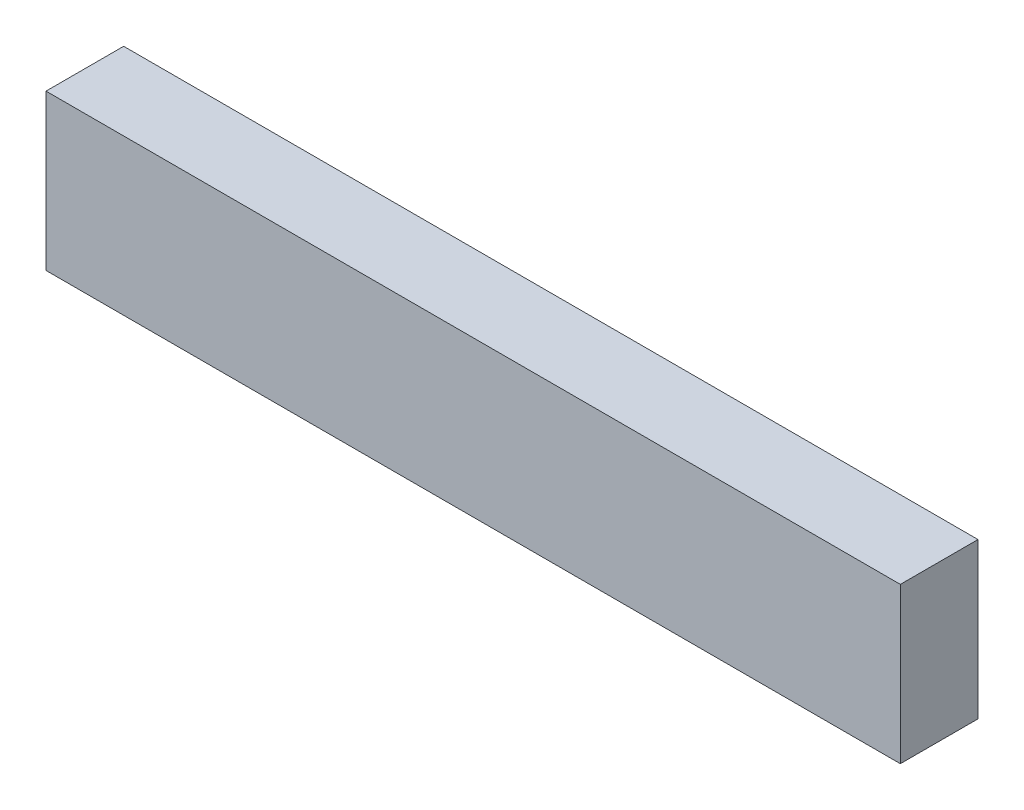
SolidWorks part; units mm, degrees
ref_plane "정면" through (0, 0, 0) normal (0, 0, 1) x (1, 0, 0)
ref_plane "윗면" through (0, 0, 0) normal (0, 1, 0) x (1, 0, 0)
ref_plane "우측면" through (0, 0, 0) normal (1, 0, 0) x (0, 0, -1)
sketch "스케치1" plane through (0, 0, 0) normal (0, 0, 1) x (1, 0, 0)
  line L1 (0, 0) -> (110, 0)
  line L2 (0, 0) -> (0, -20)
  line L3 (0, -20) -> (110, -20)
  line L4 (110, 0) -> (110, -20)
  dimension "D1" = 110
  dimension "D2" = 20
extrude "보스-돌출1" add sketch "스케치1" along normal blind 10
